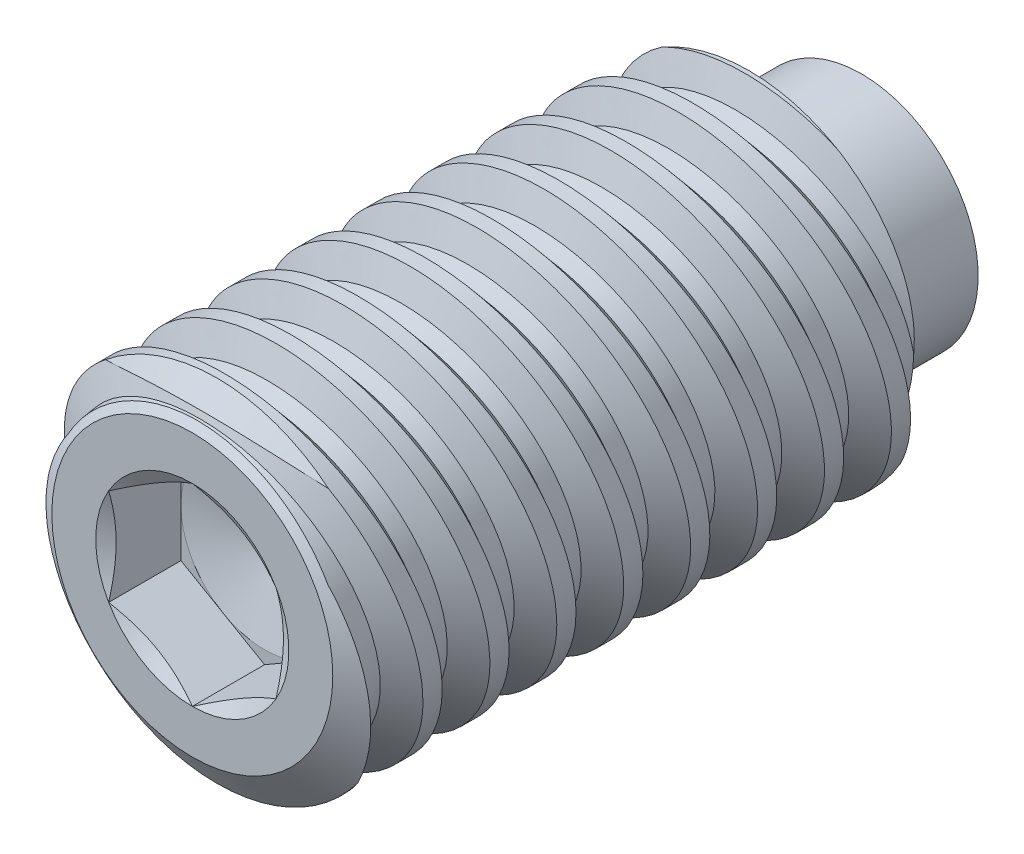
SolidWorks part; units mm, degrees
ref_plane "Front" through (0, 0, 0) normal (0, 0, 1) x (1, 0, 0)
ref_plane "Top" through (0, 0, 0) normal (0, 1, 0) x (1, 0, 0)
ref_plane "Right" through (0, 0, 0) normal (1, 0, 0) x (0, 0, -1)
sketch "Sketch22" plane through (0, 0, 0) normal (1, 0, 0) x (0, 0, -1)
  line L0 (-3.9688, 0) -> (-3.9688, 1.6662)
  line L1 (-3.9688, 1.6662) -> (-3.6771, 2.0828)
  line L2 (-3.6771, 2.0828) -> (2.636, 2.0828)
  line L3 (3.9688, 0) -> (3.9688, 1.3843)
  line L5 (3.9688, 0) -> (-3.9688, 0)
  line L6 (4.4773, 0) -> (3.9688, 0) construction
  line L7 (3.9688, 1.3843) -> (2.8766, 1.3843)
  line L11 (-3.6771, -2.0828) -> (2.636, -2.0828) construction
  line L13 (2.8766, 1.3843) -> (2.8765, 1.6662)
  line L14 (2.8765, 1.6662) -> (2.636, 2.0828)
  line L15 (-3.9688, 1.6662) -> (2.8765, 1.6662) construction
  dimension "D1" = 6.6048
  dimension "Screw Dia" = 4.1656
  dimension "D2" = 60
  dimension "Length" = 7.9375
  dimension "D3" = 35
  dimension "D7" = 3.3325
  dimension "Tip Dia" = 2.7686
  dimension "Tip Length" = 1.0922
revolve "Revolve1" add sketch "Sketch22" angle 360 about L6
sketch "Sketch6" plane through (0, 0, 0) normal (1, 0, 0) x (0, 0, -1)
  line L0 (1.8563, 2.0828) -> (2.6501, -2.0828) construction
  line L1 (-3.6771, 2.0828) -> (2.636, 2.0828) construction
  line L2 (2.636, 2.0828) -> (2.636, 2.2314) construction
  line L3 (1.8563, 2.0828) -> (1.9538, 2.1014) construction
  line L4 (2.4728, 1.7629) -> (2.2779, 1.7258)
  line L5 (2.2779, 1.7258) -> (1.9538, 2.1014)
  line L6 (2.4728, 1.7629) -> (2.636, 2.2314)
  line L7 (2.636, 2.2314) -> (1.9538, 2.1014)
  line L8 (2.3108, 2.0828) -> (3.1046, -2.0828) construction
  line L9 (3.5591, 0.1622) -> (1.8563, -0.1622) construction
  line L10 (2.2949, 2.1664) -> (2.3753, 1.7443) construction
  line L13 (1.8563, -2.0828) -> (1.8563, 2.0828) construction
  line L14 (1.8563, -2.0828) -> (2.6501, -2.0828) construction
  line L15 (2.6501, -2.0828) -> (3.1046, -2.0828) construction
  line L16 (-3.6771, -2.0828) -> (2.636, -2.0828) construction
  line L18 (1.8563, 2.0828) -> (2.3108, 2.0828) construction
  point P18 (2.7077, 0)
  dimension "D1" = 0.7937
  dimension "D2" = 0.1984
  dimension "D3" = 60
  dimension "D4" = 0.0992
  dimension "Pitch" = 0.7937
revolve "Cut-Revolve8" cut sketch "Sketch6" angle 360 about L9
pattern_linear "LPattern1" count 9 spacing 0.7937 along (0, 0, 1) count 2 spacing 0.7937 along (0, 0, 1) of "Cut-Revolve8"
sketch "Sketch23" plane through (0, 0, 3.9687) normal (0, 0, 1) x (1, 0, 0)
  line L1 (0, 1.1457) -> (-0.9922, 0.5728)
  line L2 (-0.9922, 0.5728) -> (-0.9922, -0.5728)
  line L3 (-0.9922, -0.5728) -> (0, -1.1457)
  line L4 (0, -1.1457) -> (0.9922, -0.5728)
  line L5 (0.9922, -0.5728) -> (0.9922, 0.5728)
  line L6 (0.9922, 0.5728) -> (0, 1.1457)
  circle A0 centre (0, 0) radius 0.9922 construction
  dimension "Hex" = 1.9844
extrude "Cut-Extrude10" cut sketch "Sketch23" against normal blind 0.8573
sketch "Sketch24" plane through (0, 0, 3.9687) normal (0, 0, 1) x (1, 0, 0)
  circle A0 centre (0, 0) radius 1.1457
extrude "Cut-Extrude11" cut sketch "Sketch24" against normal through all draft 60
sketch "Sketch26" plane through (0, 0, 3.1115) normal (0, 0, 1) x (1, 0, 0)
  circle A0 centre (0, 0) radius 0.9922 construction
  circle A1 centre (0, 0) radius 0.9922
extrude "Cut-Extrude12" cut sketch "Sketch26" against normal through all draft 75
equation "\"D2@Sketch6\"=\"Pitch@Sketch6\"/4"
equation "\"D4@Sketch6\"=\"Pitch@Sketch6\"/8"
equation "\"D1@Sketch6\"=\"Pitch@Sketch6\""
equation "\"D3@LPattern1\"=\"Pitch@Sketch6\""
equation "\"D1@LPattern1\"=(\"D1@Sketch22\"/\"Pitch@Sketch6\")+1"
equation "\"D4@LPattern1\"=\"Pitch@Sketch6\""
equation "\"D7@Sketch22\"=\"Screw Dia@Sketch22\"*.8"
